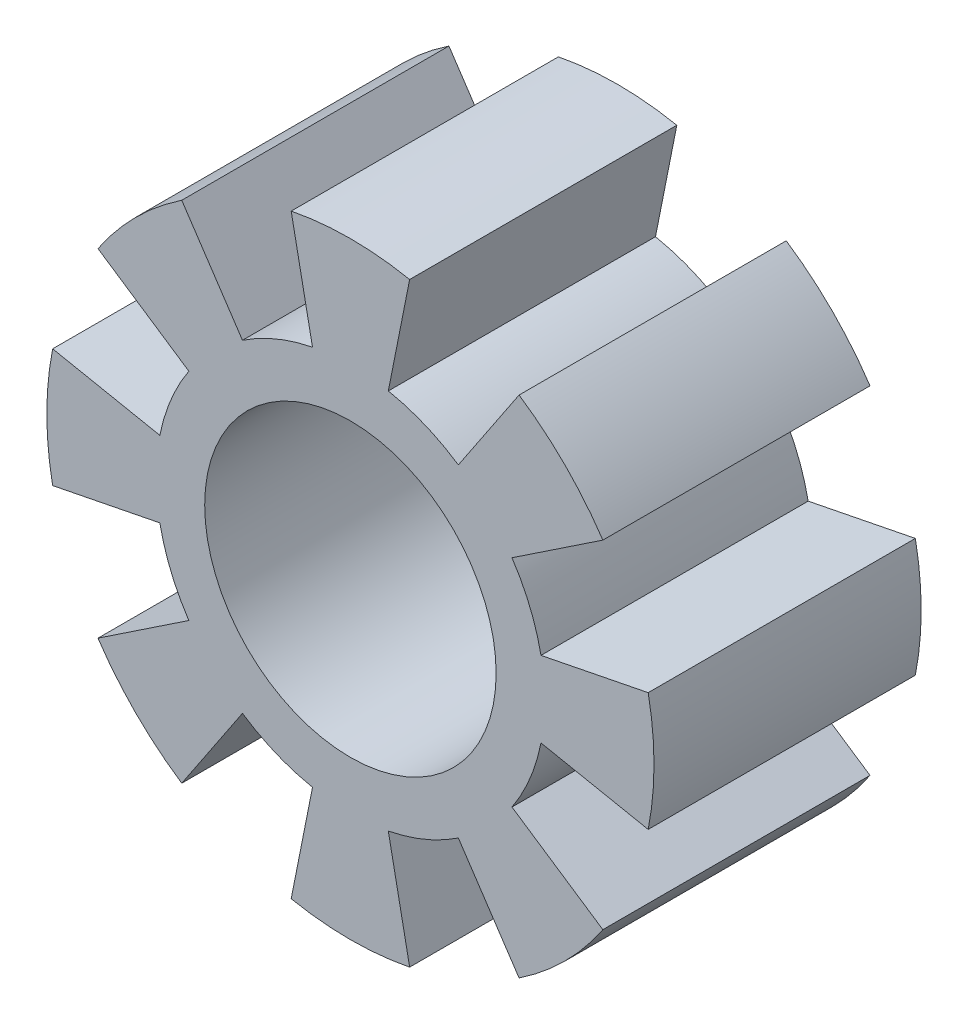
SolidWorks part; units mm, degrees
ref_plane "前视基准面" through (0, 0, 0) normal (0, 0, 1) x (1, 0, 0)
ref_plane "上视基准面" through (0, 0, 0) normal (0, 1, 0) x (1, 0, 0)
ref_plane "右视基准面" through (0, 0, 0) normal (1, 0, 0) x (0, 0, -1)
sketch "草图1" plane through (0, 0, 0) normal (0, 0, 1) x (1, 0, 0)
  line L0 (-14.4547, 0) -> (16.4529, 0) construction
  line L1 (0, 15.9609) -> (0, -13.8839) construction
  line L2 (-3.3311, 16.7463) -> (3.3311, -16.7463) construction
  line L3 (3.3311, 16.7463) -> (-3.3311, -16.7463) construction
  line L4 (-2.4386, 12.2598) -> (-1.5607, 7.8463)
  line L5 (2.4386, 12.2598) -> (1.5607, 7.8463)
  line L6 (6.9446, 10.3934) -> (4.4446, 6.6518)
  line L7 (10.3934, 6.9446) -> (6.6518, 4.4446)
  line L8 (12.2598, 2.4386) -> (7.8463, 1.5607)
  line L9 (12.2598, -2.4386) -> (7.8463, -1.5607)
  line L10 (10.3934, -6.9446) -> (6.6518, -4.4446)
  line L11 (6.9446, -10.3934) -> (4.4446, -6.6518)
  line L12 (2.4386, -12.2598) -> (1.5607, -7.8463)
  line L13 (-2.4386, -12.2598) -> (-1.5607, -7.8463)
  line L14 (-6.9446, -10.3934) -> (-4.4446, -6.6518)
  line L15 (-10.3934, -6.9446) -> (-6.6518, -4.4446)
  line L16 (-12.2598, -2.4386) -> (-7.8463, -1.5607)
  line L17 (-12.2598, 2.4386) -> (-7.8463, 1.5607)
  line L18 (-10.3934, 6.9446) -> (-6.6518, 4.4446)
  line L19 (-6.9446, 10.3934) -> (-4.4446, 6.6518)
  line L20 (0, 0) -> (1.5607, 7.8463) construction
  arc A2 (-1.5607, 7.8463) -> (-4.4446, 6.6518) centre (0, 0) ccw
  arc A4 (2.4386, 12.2598) -> (-2.4386, 12.2598) centre (0, 0) ccw
  arc A5 (10.3934, 6.9446) -> (6.9446, 10.3934) centre (0, 0) ccw
  arc A6 (12.2598, -2.4386) -> (12.2598, 2.4386) centre (0, 0) ccw
  arc A7 (6.9446, -10.3934) -> (10.3934, -6.9446) centre (0, 0) ccw
  arc A8 (-2.4386, -12.2598) -> (2.4386, -12.2598) centre (0, 0) ccw
  arc A9 (-10.3934, -6.9446) -> (-6.9446, -10.3934) centre (0, 0) ccw
  arc A10 (-12.2598, 2.4386) -> (-12.2598, -2.4386) centre (0, 0) ccw
  arc A11 (-6.9446, 10.3934) -> (-10.3934, 6.9446) centre (0, 0) ccw
  arc A12 (-6.6518, 4.4446) -> (-7.8463, 1.5607) centre (0, 0) ccw
  arc A13 (4.4446, 6.6518) -> (1.5607, 7.8463) centre (0, 0) ccw
  arc A14 (7.8463, 1.5607) -> (6.6518, 4.4446) centre (0, 0) ccw
  arc A15 (6.6518, -4.4446) -> (7.8463, -1.5607) centre (0, 0) ccw
  arc A16 (1.5607, -7.8463) -> (4.4446, -6.6518) centre (0, 0) ccw
  arc A17 (-4.4446, -6.6518) -> (-1.5607, -7.8463) centre (0, 0) ccw
  arc A18 (-7.8463, -1.5607) -> (-6.6518, -4.4446) centre (0, 0) ccw
  circle A19 centre (0, 0) radius 6
  dimension "D1" = 12
  dimension "D3" = 11.25
  dimension "D5" = 8
extrude "凸台-拉伸1" add sketch "草图1" along normal blind 11
